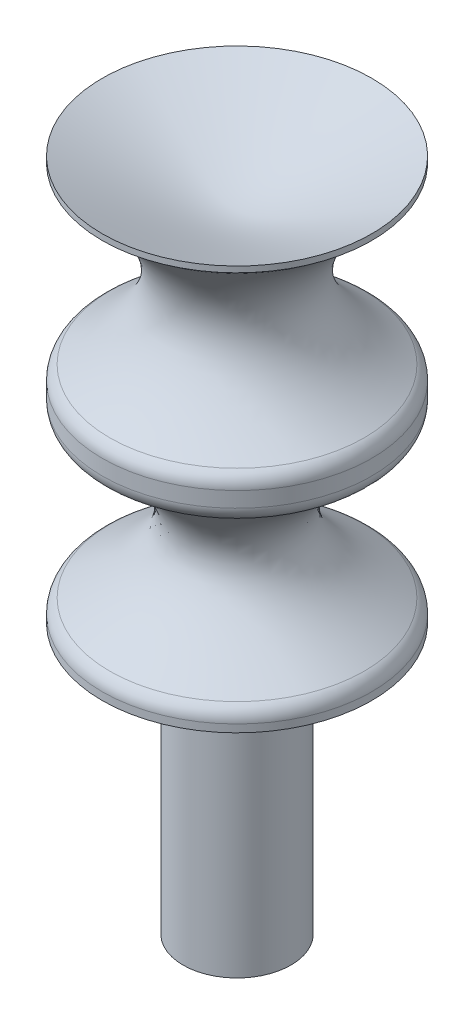
SolidWorks part; units mm, degrees
material "Brass"
ref_plane "Front Plane" through (0, 0, 0) normal (0, 0, 1) x (1, 0, 0)
ref_plane "Top Plane" through (0, 0, 0) normal (0, 1, 0) x (1, 0, 0)
ref_plane "Right Plane" through (0, 0, 0) normal (1, 0, 0) x (0, 0, -1)
sketch "Sketch1" plane through (0, 0, 0) normal (1, 0, 0) x (0, 0, -1)
  line L0 (0, 7.3903) -> (0, -9.525)
  line L1 (5.9949, -1.0222) -> (0.3551, -4.7625) construction
  line L2 (6.35, 4.7625) -> (-8.2216, 4.7625) construction
  line L3 (2.54, -9.525) -> (6.35, -9.525)
  line L4 (6.35, 9.525) -> (6.35, 9.2471)
  line L5 (-6.35, 9.525) -> (6.35, -9.525) construction
  line L6 (-6.35, -9.525) -> (6.35, 9.525) construction
  line L7 (0, 0) -> (6.35, 0) construction
  line L8 (-8.0879, -4.7625) -> (11.2295, -4.7625) construction
  line L9 (6.35, 9.2471) -> (0.1822, 4.8912) construction
  line L10 (0.1822, 4.8912) -> (5.996, 1.0219) construction
  line L11 (0.3551, -4.7625) -> (3.175, -6.6326) construction
  line L12 (6.35, 0.3612) -> (6.35, -0.3607)
  line L13 (6.35, -9.1643) -> (6.35, -9.525)
  line L14 (3.175, -6.6326) -> (5.9949, -8.5028) construction
  line L17 (0, -9.525) -> (0, -22.225)
  line L18 (0, -22.225) -> (2.54, -22.225)
  line L19 (2.54, -9.525) -> (2.54, -22.225)
  arc A0 (5.9949, -8.5028) -> (6.35, -9.1643) centre (5.5562, -9.1643) cw
  arc A1 (5.996, 1.0219) -> (6.35, 0.3612) centre (5.5562, 0.3612) cw
  arc A2 (5.9949, -1.0222) -> (6.35, -0.3607) centre (5.5562, -0.3607) ccw
  conic Q0 (0, 7.3903) -> (6.35, 9.525) control (1.5875, 7.3903) rho 0.585786
  spline S0 degree 2 poles (6.35, 9.2471) (0.1822, 4.8912) (5.996, 1.0219) knots 0 0 0 1 1 1
  spline S1 degree 3 poles (5.9949, -1.0222) (0.3551, -4.7625) (3.175, -6.6326) (5.9949, -8.5028) knots 0 0 0 0 1 1 1 1
  point P0 (0, 0)
  dimension "D3" = 0.7937
  dimension "D7" = 0.7937
  dimension "D1" = 12.7
  dimension "D2" = 19.05
  dimension "D4" = 4.7625
  dimension "D5" = 4.7625
  dimension "D6" = 0.2779
  dimension "D8" = 6.35
  dimension "D9" = 2.54
  dimension "D10" = 12.7
revolve "Revolve1" add sketch "Sketch1" angle 360 about L17
